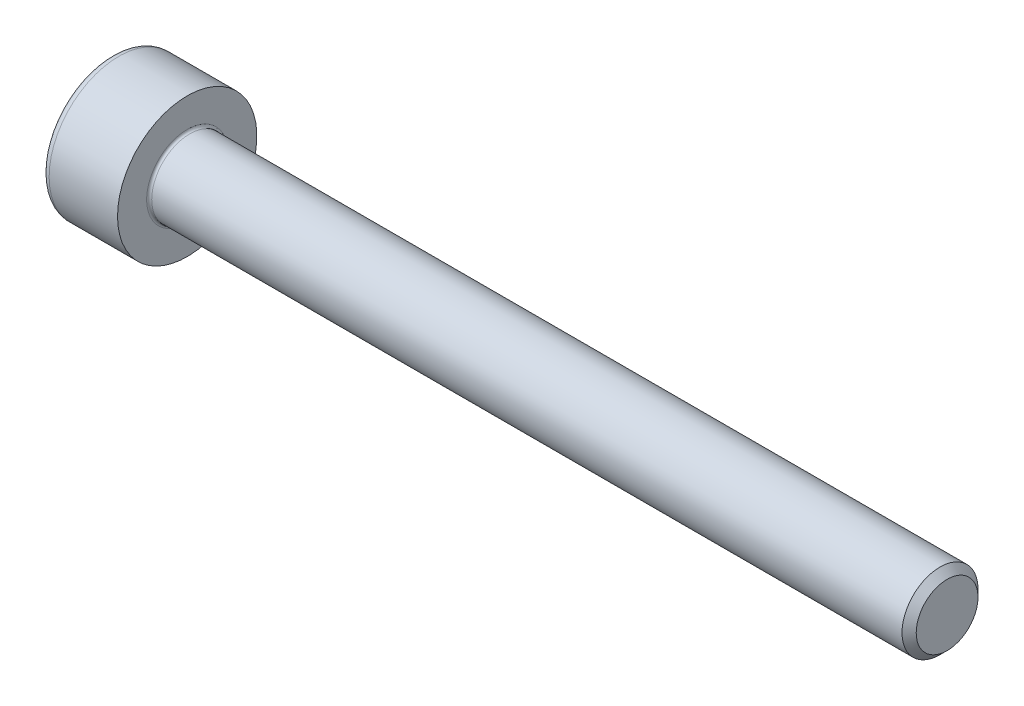
SolidWorks part; units mm, degrees
revolve "Base-Revolve" add sketch "BodySke"
sketch "BodySke" plane through (0, 0, 0) normal (0, 0, 1) x (1, 0, 0)
  line L0 (0, 0) -> (0, 2.75)
  line L1 (0, 2.75) -> (3, 2.75)
  line L2 (3, 2.75) -> (3, 1.5)
  line L3 (3, 1.5) -> (32.7195, 1.5)
  line L4 (33, 1.2195) -> (33, 0)
  line L5 (33, 0) -> (0, 0)
  line L6 (-31.75, 0) -> (127, 0) construction
  line L8 (33, 1.2195) -> (32.7195, 1.5)
  line L10 (33, -1.2195) -> (32.7195, -1.5) construction
  line L11 (3.5, 9.525) -> (3.5, 3.175) construction
  line L12 (23, 9.525) -> (23, 3.175) construction
  line L13 (17.0069, 9.525) -> (17.0069, 3.175) construction
  dimension "Head_ht" = 3
  dimension "Length" = 30
  dimension "Body_ch_ang" = 45
  dimension "Diameter" = 3
  dimension "Minor_dia" = 2.439
  dimension "Advance" = 0.5
  dimension "Thread_nom" = 10
  dimension "Thread_length" = 15.9931
  dimension "Head_dia" = 5.5
cosmetic thread "ThreadCosmetic" [suppressed]
fillet "Fillet1" radius 0.1 1 edges at (3, 0, 1.5)
fillet "Fillet2" radius 0.3 1 edges at (0, 0, 2.75)
ref_plane "Plane1" through (0, 0, 0) normal (0, 0, 1) x (1, 0, 0)
ref_plane "Plane2" through (0, 0, 0) normal (0, 1, 0) x (1, 0, 0)
ref_plane "Plane3" through (0, 0, 0) normal (1, 0, 0) x (0, 0, -1)
sketch "Sketch2" plane through (0, 0, 0) normal (0, 0, 1) x (1, 0, 0)
  line L0 (0, 1.26) -> (1.3, 1.26)
  line L1 (1.3, 1.26) -> (2.0275, 0)
  line L2 (-31.75, 0) -> (127, 0) construction
  line L3 (2.0275, 0) -> (0, 0)
  line L4 (0, 0) -> (0, 1.26)
  line L6 (0, 0) -> (47.625, 0) construction
  dimension "D1" = 1.26
  dimension "D2" = 60
  dimension "Depth" = 1.3
revolve "Hex-PreBroach" cut sketch "Sketch2" angle 360 about L6
sketch "Sketch3" plane through (0, 0, 0) normal (-1, 0, 0) x (0, 0.5, 0.866)
  line L0 (0.7275, 1.26) -> (-0.7275, 1.26)
  line L1 (-0.7275, 1.26) -> (-1.4549, 0)
  line L2 (0.7275, 1.26) -> (1.4549, 0)
  line L3 (0.7275, -1.26) -> (1.4549, 0)
  line L4 (0.7275, -1.26) -> (-0.7275, -1.26)
  line L5 (-0.7275, -1.26) -> (-1.4549, 0)
  dimension "D1" = 1.26
  dimension "D2" = 1.26
  dimension "Hex_size" = 2.52
extrude "Hex" cut sketch "Sketch3" against normal blind 1.3
sketch "ThdSchSke" plane through (0, 0, 0) normal (0, 0, 1) x (1, 0, 0)
  line L0 (23, -1.2195) -> (22.8036, -1.5)
  line L1 (23, -1.2195) -> (23.1964, -1.5)
  line L2 (23.1964, -1.5) -> (23.1964, -1.875)
  line L3 (-3.175, 0) -> (5.1513, 0) construction
  line L4 (0, 2.45) -> (0, -2.45) construction
  line L5 (23.1964, -1.875) -> (22.8036, -1.875)
  line L6 (22.8036, -1.875) -> (22.8036, -1.5)
  dimension "Thread_minor" = 2.439
  dimension "Diameter" = 3
  dimension "Start" = 23
revolve "ThreadSchematic" [suppressed] cut sketch "ThdSchSke" angle 360 about L3
pattern_linear "ThdSchPat" [suppressed]
equation "\"D2@Sketch3\" = \"Hex_size@Sketch3\" / 2"
equation "\"D1@Sketch3\" = \"Hex_size@Sketch3\" / 2"
equation "\"D1@Sketch2\" = \"Hex_size@Sketch3\" / 2"
equation "\"Thread_minor@ThreadCosmetic\"  =  \"Minor_dia@BodySke\""
equation "\"Depth@Sketch2\" =  \"Key_eng@Hex\""
equation "\"Thread_length@ThreadCosmetic\" = ((sgn( (\"Length@BodySke\" - \"Advance@BodySke\" * 3.0) - \"Thread_nom@BodySke\" )-1)*( (\"Length@BodySke\" - \"Advance@BodySke\" * 3.0) - \"Thread_nom@BodySke\" ))/-2+ \"Thread_nom@BodySke\""
equation "\"Thread_minor@ThdSchSke\" = \"Minor_dia@BodySke\""
equation "\"Diameter@ThdSchSke\" = \"Diameter@BodySke\""
equation "\"Overcut@ThdSchSke\" = \"Diameter@BodySke\" * 1.25"
equation "\"Start@ThdSchSke\" = \"Head_ht@BodySke\" + \"Length@BodySke\" - \"Thread_length@ThreadCosmetic\"  '---Non-countersunk---"
equation "\"Num_threads@ThdSchPat\" = int( \"Thread_length@ThreadCosmetic\" / \"Advance@BodySke\" + 0.999 )  + 1"
equation "\"Advance@ThdSchPat\" = \"Thread_length@ThreadCosmetic\" /  (\"Num_threads@ThdSchPat\" - 1) 'relax it"
equation "\"Num_threads@ThdSchPat\" = \"Num_threads@ThdSchPat\" - sgn( \"Num_threads@ThdSchPat\" - 1) '---chamfered tips only---"
